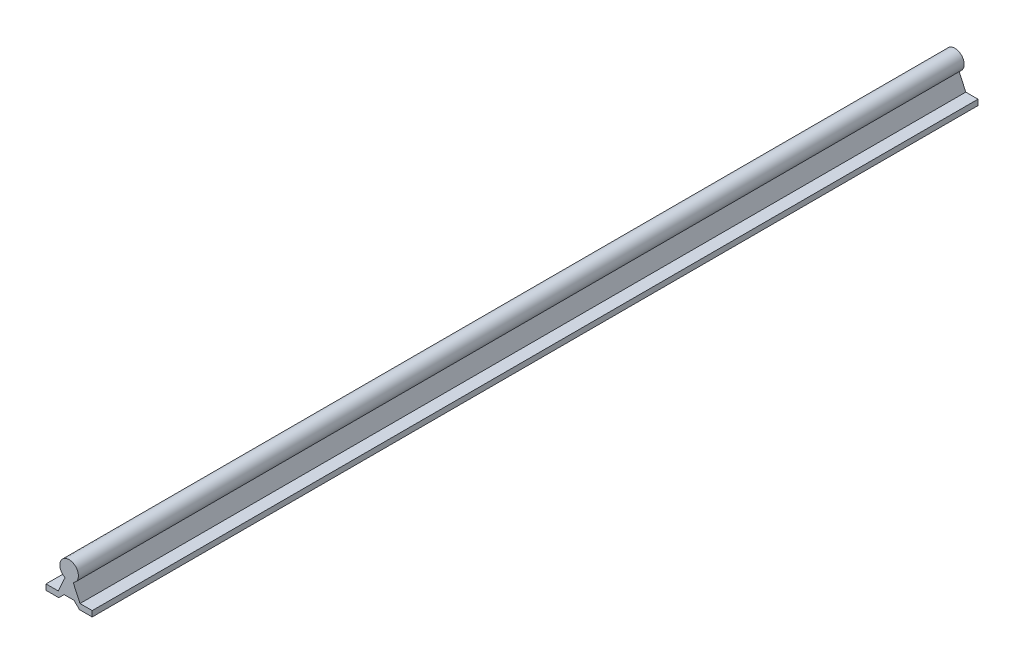
SolidWorks part; units mm, degrees
ref_plane "Front Plane" through (0, 0, 0) normal (0, 0, 1) x (1, 0, 0)
ref_plane "Top Plane" through (0, 0, 0) normal (0, 1, 0) x (1, 0, 0)
ref_plane "Right Plane" through (0, 0, 0) normal (1, 0, 0) x (0, 0, -1)
sketch "Sketch1" plane through (0, 0, 0) normal (0, 0, 1) x (1, 0, 0)
  line L0 (3.5, 17.6063) -> (9.375, 4.8)
  line L1 (19.875, 4.8) -> (9.375, 4.8)
  line L2 (19.875, 4.8) -> (19.875, 0)
  line L3 (19.875, 0) -> (8.875, 0)
  line L4 (-19.875, 4.8) -> (-19.875, 0)
  line L5 (19.875, 4.8) -> (-19.875, 0) construction
  line L6 (19.875, 0) -> (-19.875, 4.8) construction
  line L7 (-3.5, 17.6063) -> (-9.375, 4.8)
  line L8 (9.375, 4.8) -> (-9.375, 4.8) construction
  line L9 (-9.375, 4.8) -> (-19.875, 4.8)
  line L10 (-19.875, 0) -> (-8.875, 0)
  line L11 (-8.875, 0) -> (-4.275, 4.6)
  line L12 (-4.275, 4.6) -> (4.275, 4.6)
  line L13 (19.875, 0) -> (8.875, 0)
  line L14 (8.875, 0) -> (4.275, 4.6)
  line L15 (8.875, 0) -> (-8.875, 0) construction
  line L16 (-8.875, 0) -> (-19.875, 0)
  arc A0 (3.5, 17.6063) -> (-3.5, 17.6063) centre (0, 24.8) ccw
  arc A1 (-3.5, 17.6063) -> (3.5, 17.6063) centre (0, 24.8) ccw construction
  point P0 (0, 2.4)
  dimension "D1" = 16
  dimension "D2" = 24.8
  dimension "D3" = 39.75
  dimension "D4" = 4.8
  dimension "D5" = 7
  dimension "D6" = 18.75
  dimension "D7" = 4.6
  dimension "D8" = 11
  dimension "D9" = 11
  dimension "D10" = 45
extrude "Boss-Extrude1" add sketch "Sketch1" along normal blind 762 contours L0 A0 L7 L9 L4 L10 L11 L12 L14 L3 L2 L1
equation "\"length\"= 30in"
equation "\"D1@Boss-Extrude1\"=\"length\""
